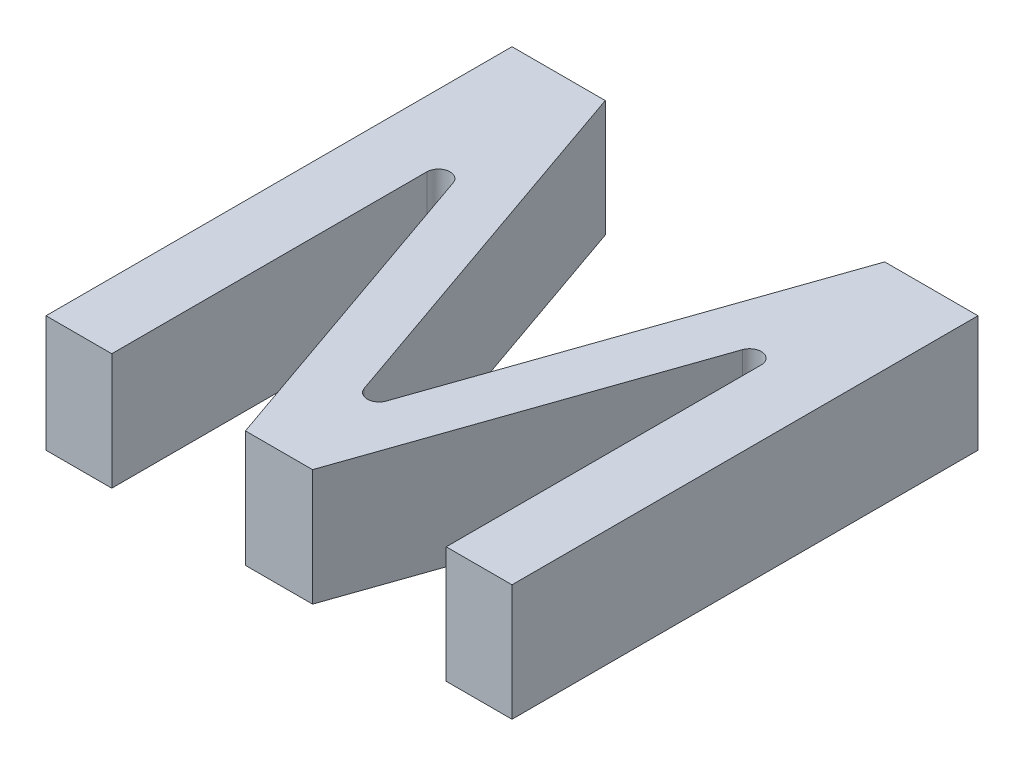
SolidWorks part; units mm, degrees
ref_plane "Front Plane" through (0, 0, 0) normal (0, 0, 1) x (1, 0, 0)
ref_plane "Top Plane" through (0, 0, 0) normal (0, 1, 0) x (1, 0, 0)
ref_plane "Right Plane" through (0, 0, 0) normal (1, 0, 0) x (0, 0, -1)
sketch "Sketch1" plane through (0, 0, 0) normal (0, 1, 0) x (1, 0, 0)
  line L0 (5.6457, 32.9544) -> (17.1192, 0)
  line L1 (0, 0) -> (5.6457, 0)
  line L2 (0, 0) -> (0, 40)
  line L3 (0, 40) -> (8.0046, 40)
  line L4 (40, 0) -> (40, 40)
  line L5 (0, 40) -> (8.0046, 40)
  line L6 (8.0046, 40) -> (20, 5.5465)
  line L7 (5.6457, 32.9544) -> (5.6457, 0)
  line L8 (5.6457, 32.9544) -> (17.1192, 0)
  line L9 (31.9954, 40) -> (20, 5.5465)
  line L10 (34.3543, 32.9544) -> (22.8808, 0)
  line L11 (34.3543, 32.9544) -> (34.3543, 0)
  line L12 (31.9954, 40) -> (40, 40)
  line L13 (17.1192, 0) -> (22.8808, 0)
  line L14 (34.3543, 0) -> (40, 0)
  line L15 (17.1192, 0) -> (22.8808, 0)
  line L16 (22.8808, 0) -> (34.3543, 32.9544)
  line L17 (34.3543, 32.9544) -> (34.3543, 0)
  line L18 (34.3543, 0) -> (40, 0)
  line L19 (40, 0) -> (40, 40)
  line L20 (40, 40) -> (31.9954, 40)
  line L21 (31.9954, 40) -> (20, 5.5465)
  line L22 (20, 5.5465) -> (8.0046, 40)
  line L23 (8.0046, 40) -> (0, 40)
  line L24 (0, 40) -> (0, 0)
  line L25 (0, 0) -> (5.6457, 0)
  dimension "D1" = 40
  dimension "D2" = 40
extrude "Boss-Extrude1" add sketch "Sketch1" along normal blind 10 contours L11 L14 L4 L12 L9 L6 L3 L2 L1 L7 L0 L13 L10
fillet "Fillet1" radius 1 3 edges at (34.3543, 5, -32.9544) (5.6457, 5, -32.9544) (20, 5, -5.5465)
